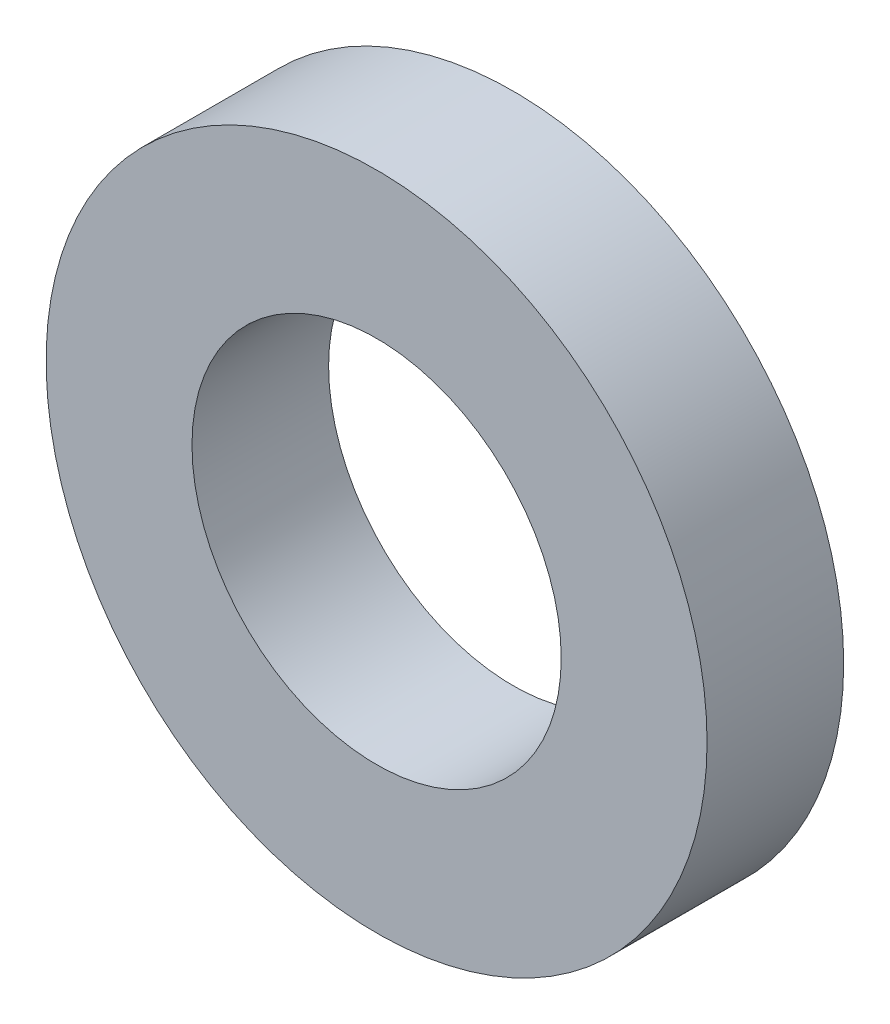
SolidWorks part; units mm, degrees
ref_plane "Front Plane" through (0, 0, 0) normal (0, 0, 1) x (1, 0, 0)
ref_plane "Top Plane" through (0, 0, 0) normal (0, 1, 0) x (1, 0, 0)
ref_plane "Right Plane" through (0, 0, 0) normal (1, 0, 0) x (0, 0, -1)
sketch "Sketch1" plane through (0, 0, 0) normal (0, 0, 1) x (1, 0, 0)
  circle A0 centre (0, 0) radius 5
  circle A1 centre (0, 0) radius 8.95
  dimension "D1" = 17.9
  dimension "D2" = 10
extrude "Boss-Extrude1" add sketch "Sketch1" along normal blind 3.7
